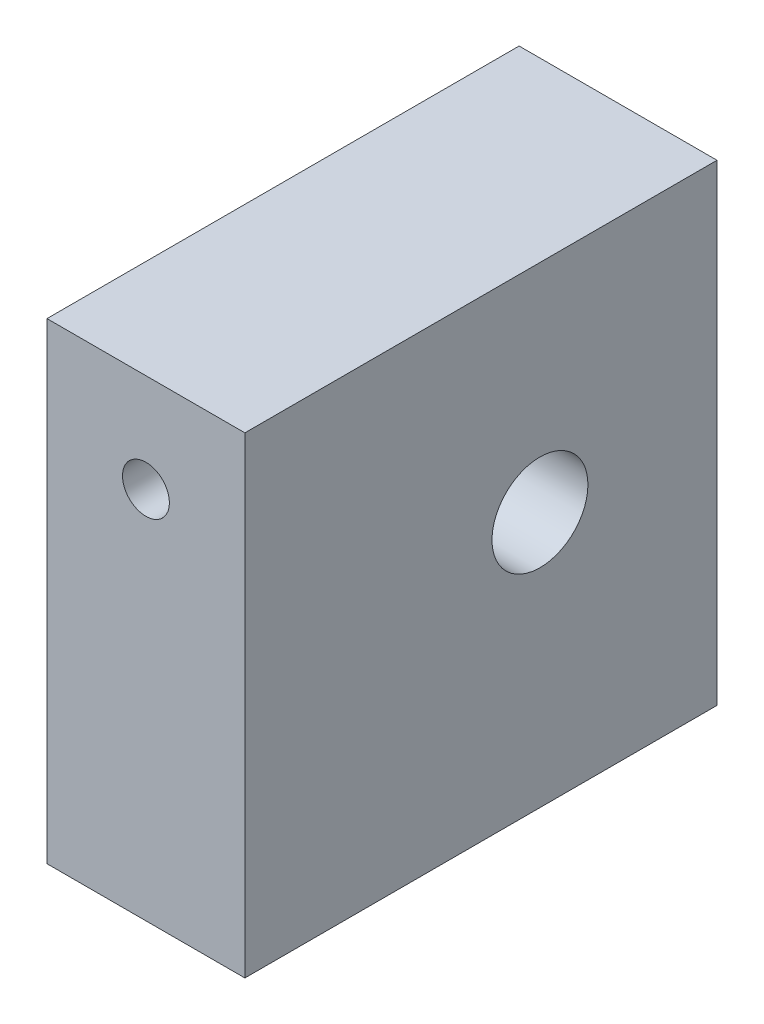
SolidWorks part; units mm, degrees
material "6061-T4 (SS)"
ref_plane "Front Plane" through (0, 0, 0) normal (0, 0, 1) x (1, 0, 0)
ref_plane "Top Plane" through (0, 0, 0) normal (0, 1, 0) x (1, 0, 0)
ref_plane "Right Plane" through (0, 0, 0) normal (1, 0, 0) x (0, 0, -1)
sketch "Sketch1" plane through (0, 0, 0) normal (1, 0, 0) x (0, 0, -1)
  line L1 (0, 0) -> (12, 0)
  line L2 (0, 0) -> (0, 12)
  line L3 (0, 12) -> (12, 12)
  line L4 (12, 0) -> (12, 12)
  dimension "D1" = 12
  dimension "D2" = 12
extrude "Boss-Extrude1" add sketch "Sketch1" along normal blind 5.03
sketch "Sketch2" plane through (5.03, 0, 0) normal (1, 0, 0) x (0, 0, -1)
  line L0 (8.1944, 12) -> (8.1944, 6.542) construction
  line L1 (12, 12) -> (0, 12) construction
  line L2 (0, 12) -> (0, 0) construction
  point P2 (7.5, 6.5)
  dimension "D1" = 8.1944
  dimension "D2" = 5.458
sketch "Sketch3" plane through (0, 0, 0) normal (0, 0, 1) x (1, 0, 0)
  line L0 (2.515, 12) -> (2.515, 9.5) construction
  line L1 (5.03, 12) -> (0, 12) construction
  dimension "D1" = 2.5
hole_wizard "Tap Drill for #0-80 Tap1" positions "Sketch5" profile "Sketch4" hole size "#0-80" standard "ANSI Inch"
sketch "Sketch5" plane through (0, 0, 0) normal (0, 0, 1) x (1, 0, 0)
  point P0 (2.515, 9.5)
sketch "Sketch4" plane through (2.515, 9.5, 0) normal (1, 0, 0) x (0, -1, 0)
  line L0 (0, 0) -> (0, 4.3579)
  line L1 (0, 4.3579) -> (0.5956, 4)
  line L2 (0.5956, 4) -> (0.5956, 0)
  line L5 (0.5956, 0) -> (0, 0)
  line L10 (0, 4.3579) -> (-0.5956, 4) construction
  line L11 (0, -6.35) -> (0, 107.95) construction
  dimension "Hole Dia." = 1.1913
  dimension "Hole Depth" = 4
  dimension "Drill Angle" = 118
hole_wizard "#2 Clearance Hole1" positions "Sketch6" profile "Sketch7" hole size "#2" standard "ANSI Inch" end condition through all
sketch "Sketch6" plane through (5.03, 0, 0) normal (1, 0, 0) x (0, 0, -1)
  point P5 (7.5, 6.5)
sketch "Sketch7" plane through (5.03, 6.5, -7.5) normal (0, 1, 0) x (0, 0, -1)
  line L0 (0, 0) -> (0, 5.03)
  line L1 (0, 5.03) -> (1.2192, 5.03)
  line L2 (1.2192, 5.03) -> (1.2192, 0)
  line L5 (1.2192, 0) -> (0, 0)
  line L11 (0, -6.35) -> (0, 107.95) construction
  dimension "Thru Hole Dia." = 2.4384
  dimension "Thru Hole Depth" = 5.03
